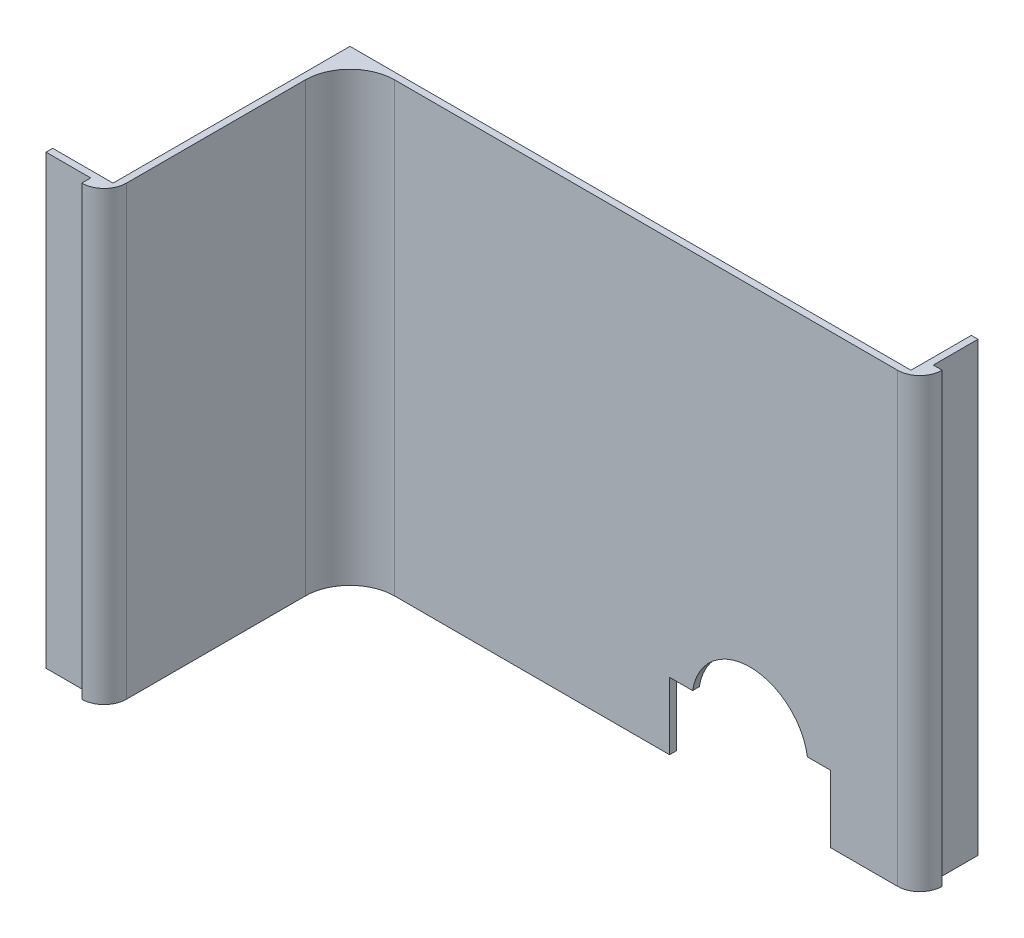
SolidWorks part; units mm, degrees
material "ABS"
ref_plane "Спереди" through (0, 0, 0) normal (0, 0, 1) x (1, 0, 0)
ref_plane "Сверху" through (0, 0, 0) normal (0, 1, 0) x (1, 0, 0)
ref_plane "Справа" through (0, 0, 0) normal (1, 0, 0) x (0, 0, -1)
sketch "Эскиз1" plane through (0, 0, 0) normal (0, 1, 0) x (1, 0, 0)
  line L0 (0, 0) -> (-112.5, 0)
  line L1 (-122.5, -10) -> (-122.5, -50)
  line L2 (-127.5, -55) -> (-127.5, -53)
  line L3 (-127.5, -53) -> (-137.5, -53)
  line L4 (5, 5) -> (3, 5)
  line L5 (3, 5) -> (3, 15)
  line L6 (3, 15) -> (1.5, 15)
  line L7 (0, 0) -> (0, 1.5) construction
  line L8 (1.5, 15) -> (1.5, 1.5)
  line L9 (-122.5, -50) -> (-124, -50) construction
  line L10 (-137.5, -53) -> (-137.5, -51.5)
  line L11 (-137.5, -51.5) -> (-124, -51.5)
  line L12 (-124, -51.5) -> (-124, 1.5)
  line L13 (-124, 1.5) -> (1.5, 1.5)
  arc A0 (-112.5, 0) -> (-122.5, -10) centre (-112.5, -10) ccw
  arc A1 (-122.5, -50) -> (-127.5, -55) centre (-127.5, -50) cw
  arc A2 (0, 0) -> (5, 5) centre (0, 5) ccw
  dimension "D1" = 112.5
  dimension "D2" = 5
  dimension "D6" = 10
  dimension "D9" = 5
  dimension "D3" = 2
  dimension "D4" = 1.5
  dimension "D5" = 1.5
  dimension "D7" = 1.5
  dimension "D8" = 40
  dimension "D10" = 2
  dimension "D11" = 1.5
  dimension "D12" = 10
  dimension "D13" = 10
extrude "Бобышка-Вытянуть1" add sketch "Эскиз1" along normal blind 100
sketch "Эскиз4" plane through (0, 0, 0) normal (0, 0, 1) x (1, 0, 0)
  line L0 (5, 0) -> (-15, 0) construction
  line L1 (-15, 0) -> (-51, 0)
  line L2 (-112.5, 0) -> (0, 0) construction
  line L3 (-51, 0) -> (-51, 15)
  line L4 (-51, 15) -> (-51, 13) construction
  line L5 (-51, 15) -> (-45.8452, 15)
  line L6 (-15, 0) -> (-15, 14.9972)
  line L7 (-15, 14.9972) -> (-20.1543, 14.9972)
  line L8 (-51, 13) -> (-15, 13) construction
  arc A0 (-45.8452, 15) -> (-20.1543, 14.9972) centre (-33, 13) cw
  dimension "D4" = 13
  dimension "D1" = 20
  dimension "D2" = 36
  dimension "D3" = 15
  dimension "D5" = 2
  dimension "D6" = 14.9972
extrude "Вырез-Вытянуть1" cut sketch "Эскиз4" against normal through all
